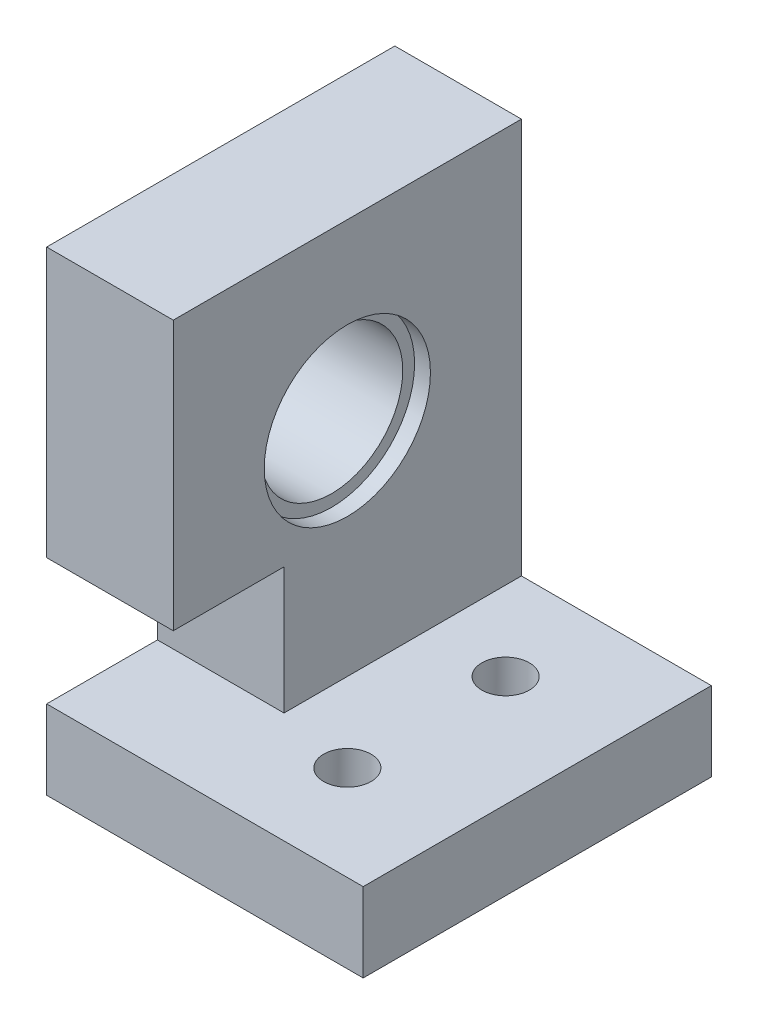
SolidWorks part; units mm, degrees
material "1060 合金"
ref_plane "前视基准面" through (0, 0, 0) normal (0, 0, 1) x (1, 0, 0)
ref_plane "上视基准面" through (0, 0, 0) normal (0, 1, 0) x (1, 0, 0)
ref_plane "右视基准面" through (0, 0, 0) normal (1, 0, 0) x (0, 0, -1)
sketch "草图1" plane through (0, 0, 0) normal (1, 0, 0) x (0, 0, -1)
  line L1 (-11, 17) -> (29, 17)
  line L2 (-11, 17) -> (-11, -6)
  line L3 (-11, -6) -> (29, -6)
  line L4 (29, 17) -> (29, -6)
  circle A6 centre (0, 0) radius 4.5
  circle A7 centre (18, 6) radius 4.5
  dimension "D4" = 9
  dimension "D5" = 9
  dimension "D7" = 11
  dimension "D6" = 11
  dimension "D8" = 18
  dimension "D9" = 6
  dimension "D10" = 11
extrude "凸台-拉伸1" add sketch "草图1" along normal blind 8
sketch "草图2" plane through (0, 0, 0) normal (-1, 0, 0) x (0, 0, 1)
  circle A0 centre (-18, 6) radius 5.25
  circle A1 centre (0, 0) radius 5.25
extrude "切除-拉伸1" cut sketch "草图2" against normal blind 1
sketch "草图3" plane through (8, 0, 0) normal (1, 0, 0) x (0, 0, -1)
  line L0 (-11, -6) -> (29, -6) construction
  line L1 (29, 17) -> (11, 17)
  line L2 (29, 17) -> (29, -6)
  line L3 (29, -6) -> (11, -6)
  line L4 (11, 11) -> (11, -6)
  line L6 (-11, 17) -> (11, 17)
  line L7 (-11, 17) -> (-11, 11)
  line L8 (-11, 11) -> (11, 11)
  circle A0 centre (0, 0) radius 4.5 construction
  dimension "D2" = 11
  dimension "D1" = 11
extrude "切除-拉伸2" cut sketch "草图3" against normal through all
sketch "草图5" plane through (8, 0, 0) normal (1, 0, 0) x (0, 0, -1)
  circle A0 centre (0, 0) radius 5.25
  dimension "D1" = 10.5
extrude "切除-拉伸3" cut sketch "草图5" against normal blind 1
sketch "草图6" plane through (8, 0, 0) normal (1, 0, 0) x (0, 0, -1)
  line L0 (11, -8.8844) -> (11, -17.8185) construction
  line L1 (-11, -6) -> (11, -6)
  line L2 (-11, -6) -> (-11, -1)
  line L3 (-11, -1) -> (11, -1)
  line L4 (11, -6) -> (11, -1)
  dimension "D1" = 5
extrude "凸台-拉伸3" add sketch "草图6" along normal blind 6
sketch "草图7" plane through (0, -6, 0) normal (0, -1, 0) x (1, 0, 0)
  line L0 (0, 11) -> (0, -11) construction
  line L1 (14, -11) -> (3, -11)
  line L2 (14, -11) -> (14, -7)
  line L3 (14, -7) -> (3, -7)
  line L4 (3, -11) -> (3, -7)
  dimension "D1" = 3
  dimension "D2" = 4
extrude "凸台-拉伸4" add sketch "草图7" along normal blind 4
sketch "草图11" plane through (0, 0, -11) normal (0, 0, -1) x (-1, 0, 0)
  line L0 (-8, -1) -> (-8, 11)
  line L1 (-8, 11) -> (-14, -1)
  line L2 (-14, -1) -> (-8, -1)
  line L3 (-8, -8.8844) -> (-8, -17.8185) construction
  dimension "D1" = 12
extrude "凸台-拉伸6" add sketch "草图11" against normal blind 3
sketch "草图12" plane through (0, -6, 0) normal (0, -1, 0) x (1, 0, 0)
  line L0 (0, 11) -> (0, -11) construction
  line L1 (8, -11) -> (0, -11)
  line L2 (8, -11) -> (8, 4)
  line L3 (8, 4) -> (0, 4)
  line L4 (0, -11) -> (0, 4)
  dimension "D1" = 15
extrude "凸台-拉伸7" add sketch "草图12" along normal blind 13
sketch "草图13" plane through (8, 0, 0) normal (1, 0, 0) x (0, 0, -1)
  line L1 (11, -19) -> (-11, -19)
  line L2 (11, -19) -> (11, -14)
  line L3 (11, -14) -> (-11, -14)
  line L4 (-11, -19) -> (-11, -14)
  dimension "D1" = 5
  dimension "D2" = 22
extrude "凸台-拉伸8" add sketch "草图13" along normal blind 10
sketch "草图14" plane through (0, -1, 0) normal (0, 1, 0) x (1, 0, 0)
  line L1 (14, -11) -> (8, -11)
  line L2 (14, -11) -> (14, 11)
  line L3 (14, 11) -> (8, 11)
  line L4 (8, -11) -> (8, 11)
extrude "切除-拉伸9" cut sketch "草图14" against normal blind 10 and the other way through all
sketch "草图15" plane through (0, -14, 0) normal (0, 1, 0) x (-1, 0, 0)
  line L0 (-18, -11) -> (-8, -11) construction
  line L1 (-18, 11) -> (-8, 11) construction
  line L2 (-8, 11) -> (-8, -11) construction
  circle A0 centre (-13, -5) radius 1.5
  circle A1 centre (-13, 5) radius 1.5
  dimension "D1" = 3
  dimension "D2" = 6
  dimension "D3" = 6
  dimension "D4" = 5
  dimension "D5" = 5
extrude "切除-拉伸10" cut sketch "草图15" against normal through all
sketch "草图16" plane through (0, -19, 0) normal (0, -1, 0) x (1, 0, 0)
  line L1 (16.2043, 5) -> (14.6021, 7.775)
  line L2 (14.6021, 7.775) -> (11.3979, 7.775)
  line L3 (11.3979, 7.775) -> (9.7957, 5)
  line L4 (9.7957, 5) -> (11.3979, 2.225)
  line L5 (11.3979, 2.225) -> (14.6021, 2.225)
  line L6 (14.6021, 2.225) -> (16.2043, 5)
  line L7 (16.2043, -5) -> (14.6021, -2.225)
  line L8 (14.6021, -2.225) -> (11.3979, -2.225)
  line L9 (11.3979, -2.225) -> (9.7957, -5)
  line L10 (9.7957, -5) -> (11.3979, -7.775)
  line L11 (11.3979, -7.775) -> (14.6021, -7.775)
  line L12 (14.6021, -7.775) -> (16.2043, -5)
  circle A0 centre (13, 5) radius 2.775 construction
  circle A1 centre (13, -5) radius 2.775 construction
  dimension "D1" = 5.55
  dimension "D2" = 5.55
extrude "切除-拉伸11" cut sketch "草图16" against normal blind 2.5
sketch "草图17" plane through (18, 0, 0) normal (1, 0, 0) x (0, 0, -1)
  line L1 (-11, -19) -> (11, -19)
  line L2 (-11, -19) -> (-11, -14)
  line L3 (-11, -14) -> (11, -14)
  line L4 (11, -19) -> (11, -14)
extrude "凸台-拉伸9" add sketch "草图17" along normal blind 2
sketch "草图18" plane through (0, 0, 4) normal (0, 0, 1) x (1, 0, 0)
  line L0 (0, -19) -> (0, -6) construction
  line L1 (8, -19) -> (0, -19)
  line L2 (8, -19) -> (8, -14)
  line L3 (8, -14) -> (0, -14)
  line L4 (0, -19) -> (0, -14)
  dimension "D1" = 5
extrude "凸台-拉伸10" add sketch "草图18" along normal through all
